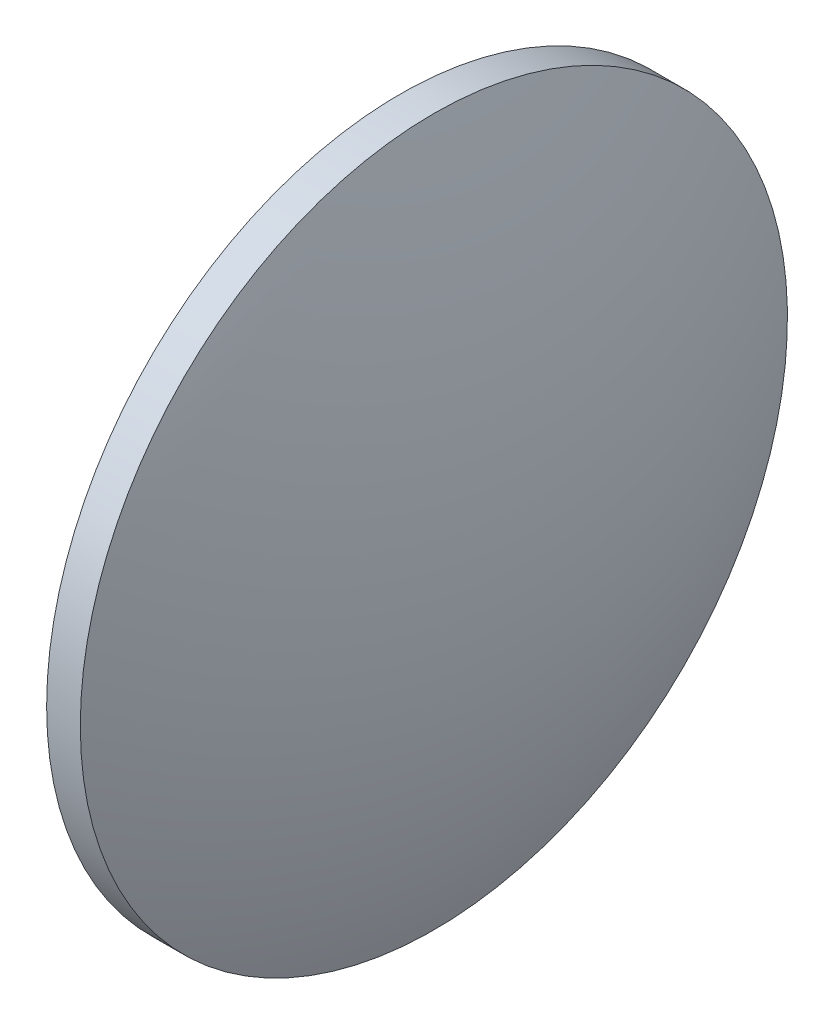
SolidWorks part; units mm, degrees
ref_plane "前视基准面" through (0, 0, 0) normal (0, 0, 1) x (1, 0, 0)
ref_plane "上视基准面" through (0, 0, 0) normal (0, 1, 0) x (1, 0, 0)
ref_plane "右视基准面" through (0, 0, 0) normal (1, 0, 0) x (0, 0, -1)
sketch "草图1" plane through (0, 0, 0) normal (0, 0, 1) x (1, 0, 0)
  line L0 (444.6403, 80.8213) -> (485.2174, 80.8213) construction
  line L1 (452.611, 80.8213) -> (452.611, 112.3213)
  line L2 (452.611, 112.3213) -> (455.611, 112.3213)
  line L3 (461.851, 80.8213) -> (452.611, 80.8213)
  arc A0 (461.851, 80.8213) -> (455.611, 112.3213) centre (379.2238, 80.8213) ccw
revolve "旋转1" add sketch "草图1" angle 360 about L0
